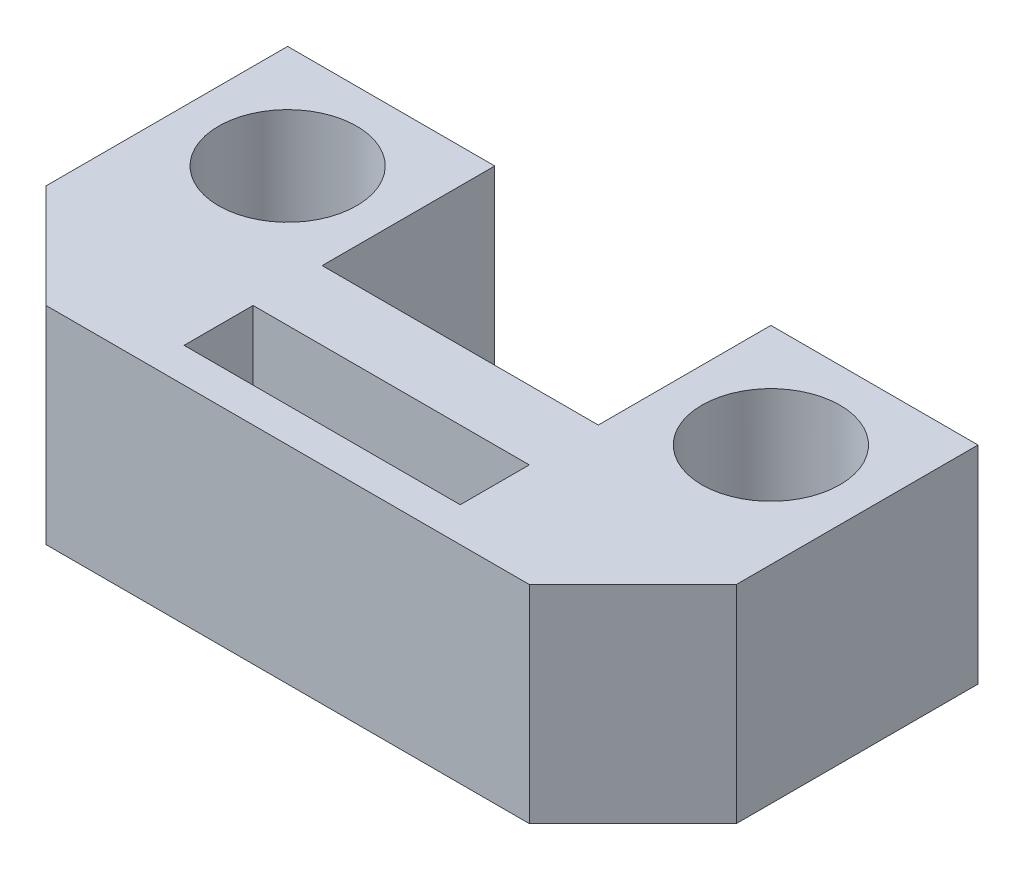
SolidWorks part; units mm, degrees
ref_plane "前视基准面" through (0, 0, 0) normal (0, 0, 1) x (1, 0, 0)
ref_plane "上视基准面" through (0, 0, 0) normal (0, 1, 0) x (1, 0, 0)
ref_plane "右视基准面" through (0, 0, 0) normal (1, 0, 0) x (0, 0, -1)
sketch "草图1" plane through (0, 0, 0) normal (0, 1, 0) x (1, 0, 0)
  line L0 (-4, 5) -> (-4, 10)
  line L1 (-10, 0) -> (10, 0)
  line L2 (-10, 0) -> (-10, 5)
  line L3 (-4, 5) -> (4, 5)
  line L4 (10, 0) -> (10, 5)
  line L5 (-4, 10) -> (-10, 10)
  line L6 (-10, 10) -> (-10, 5)
  line L7 (0, 0) -> (0, 5) construction
  line L8 (4, 5) -> (4, 10)
  line L9 (4, 10) -> (10, 10)
  line L10 (10, 10) -> (10, 5)
  dimension "D1" = 5
  dimension "D2" = 4
  dimension "D3" = 5
  dimension "D4" = 6
extrude "凸台-拉伸1" add sketch "草图1" along normal blind 6
sketch "草图2" plane through (0, 6, 0) normal (0, 1, 0) x (1, 0, 0)
  line L0 (0, 0) -> (0, 5) construction
  line L1 (-10, 0) -> (10, 0) construction
  line L2 (4, 5) -> (-4, 5) construction
  line L4 (-4, 10) -> (-10, 10) construction
  line L5 (-10, 10) -> (-10, 0) construction
  line L6 (4, 3) -> (4, 1)
  line L7 (-4, 3) -> (4, 3)
  line L8 (-4, 3) -> (-4, 1)
  line L9 (-4, 1) -> (4, 1)
  circle A0 centre (-7, 7) radius 2
  circle A1 centre (7, 7) radius 2
  point P17 (0, 1)
  point P20 (0, 3)
  dimension "D1" = 4
  dimension "D2" = 3
  dimension "D3" = 3
  dimension "D4" = 2
  dimension "D5" = 4
  dimension "D6" = 2
extrude "切除-拉伸3" cut sketch "草图2" against normal up to next
chamfer "倒角1" distance 3 angle 45 2 edges at (10, 3, 0) (-10, 3, 0)
